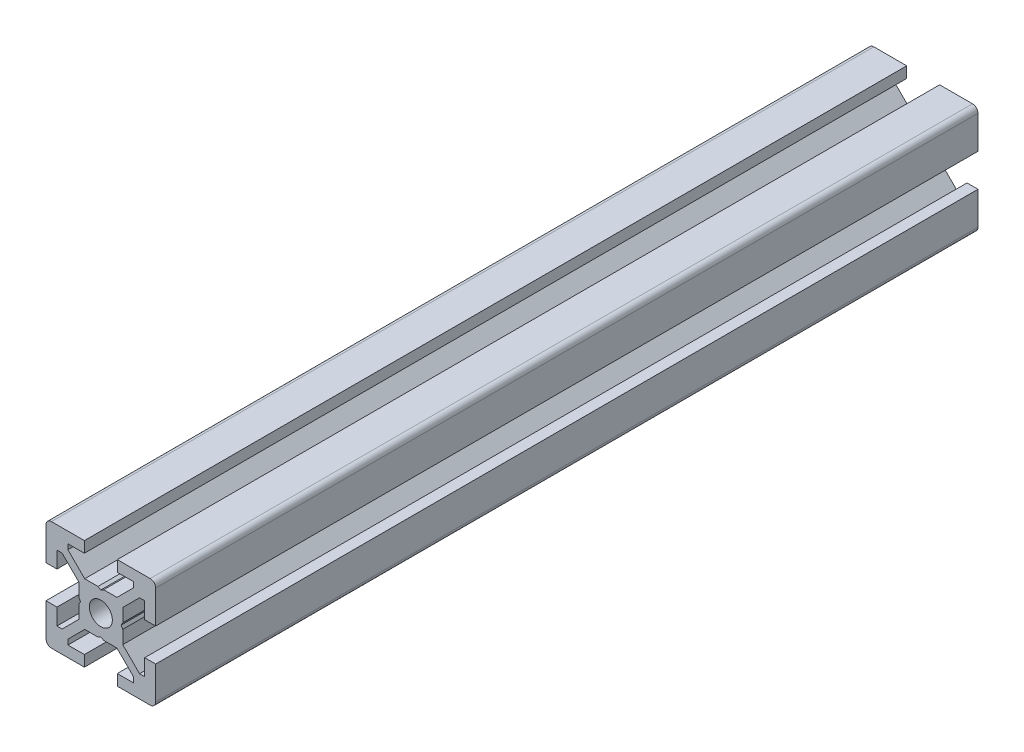
SolidWorks part; units mm, degrees
material "2014 合金"
ref_plane "正面" through (0, 0, 0) normal (0, 0, 1) x (1, 0, 0)
ref_plane "平面" through (0, 0, 0) normal (0, 1, 0) x (1, 0, 0)
ref_plane "右側面" through (0, 0, 0) normal (1, 0, 0) x (0, 0, -1)
ref_plane "平面1" through (0, 0, 0) normal (0, 0, 1) x (1, 0, 0)
sketch "ｽｹｯﾁ1" plane through (0, 0, 0) normal (0, 0, 1) x (1, 0, 0)
  line L0 (-10, -3) -> (-10, -9)
  line L1 (-9, -10) -> (-3, -10)
  line L2 (-3, -10) -> (-3, -8)
  line L3 (-3, -8) -> (-6, -8)
  line L4 (-6, -8) -> (-6, -7.0607)
  line L5 (-6, -7.0607) -> (-2.9393, -4)
  line L6 (-2.9393, -4) -> (-0.5196, -4)
  line L7 (-0.5196, -4) -> (0, -3.7)
  line L8 (0, -3.7) -> (0.5196, -4)
  line L9 (0.5196, -4) -> (2.9393, -4)
  line L10 (2.9393, -4) -> (6, -7.0607)
  line L11 (6, -7.0607) -> (6, -8)
  line L12 (6, -8) -> (3, -8)
  line L13 (3, -8) -> (3, -10)
  line L14 (3, -10) -> (9, -10)
  line L15 (10, -9) -> (10, -3)
  line L16 (10, -3) -> (8, -3)
  line L17 (8, -3) -> (8, -6)
  line L18 (8, -6) -> (7.0607, -6)
  line L19 (7.0607, -6) -> (4, -2.9393)
  line L20 (4, -2.9393) -> (4, -0.5196)
  line L21 (4, -0.5196) -> (3.7, 0)
  line L22 (3.7, 0) -> (4, 0.5196)
  line L23 (4, 0.5196) -> (4, 2.9393)
  line L24 (4, 2.9393) -> (7.0607, 6)
  line L25 (7.0607, 6) -> (8, 6)
  line L26 (8, 6) -> (8, 3)
  line L27 (8, 3) -> (10, 3)
  line L28 (10, 3) -> (10, 9)
  line L29 (9, 10) -> (3, 10)
  line L30 (3, 10) -> (3, 8)
  line L31 (3, 8) -> (6, 8)
  line L32 (6, 8) -> (6, 7.0607)
  line L33 (6, 7.0607) -> (2.9393, 4)
  line L34 (2.9393, 4) -> (0.5196, 4)
  line L35 (0.5196, 4) -> (0, 3.7)
  line L36 (0, 3.7) -> (-0.5196, 4)
  line L37 (-0.5196, 4) -> (-2.9393, 4)
  line L38 (-2.9393, 4) -> (-6, 7.0607)
  line L39 (-6, 7.0607) -> (-6, 8)
  line L40 (-6, 8) -> (-3, 8)
  line L41 (-3, 8) -> (-3, 10)
  line L42 (-3, 10) -> (-9, 10)
  line L43 (-10, 9) -> (-10, 3)
  line L44 (-10, 3) -> (-8, 3)
  line L45 (-8, 3) -> (-8, 6)
  line L46 (-8, 6) -> (-7.0607, 6)
  line L47 (-7.0607, 6) -> (-4, 2.9393)
  line L48 (-4, 2.9393) -> (-4, 0.5196)
  line L49 (-4, 0.5196) -> (-3.7, 0)
  line L50 (-3.7, 0) -> (-4, -0.5196)
  line L51 (-4, -0.5196) -> (-4, -2.9393)
  line L52 (-4, -2.9393) -> (-7.0607, -6)
  line L53 (-7.0607, -6) -> (-8, -6)
  line L54 (-8, -6) -> (-8, -3)
  line L55 (-8, -3) -> (-10, -3)
  arc A0 (-10, -9) -> (-9, -10) centre (-9, -9) ccw
  arc A1 (9, -10) -> (10, -9) centre (9, -9) ccw
  arc A2 (10, 9) -> (9, 10) centre (9, 9) ccw
  arc A3 (-9, 10) -> (-10, 9) centre (-9, 9) ccw
extrude "ﾎﾞｽ - 押し出し1" add sketch "ｽｹｯﾁ1" against normal blind 150
ref_plane "平面2" through (0, 0, 0) normal (1, 0, 0) x (0, 0, -1)
sketch "ｽｹｯﾁ2" plane through (0, 0, 0) normal (1, 0, 0) x (0, 0, -1)
  line L0 (0, 0) -> (0, 2.1)
  line L1 (0, 2.1) -> (260, 2.1)
  line L2 (260, 2.1) -> (260, 0)
  line L3 (260, 0) -> (0, 0)
  line L4 (260, 0) -> (0, 0) construction
revolve "ｶｯﾄ - 回転1" cut sketch "ｽｹｯﾁ2" angle 360 about L4
